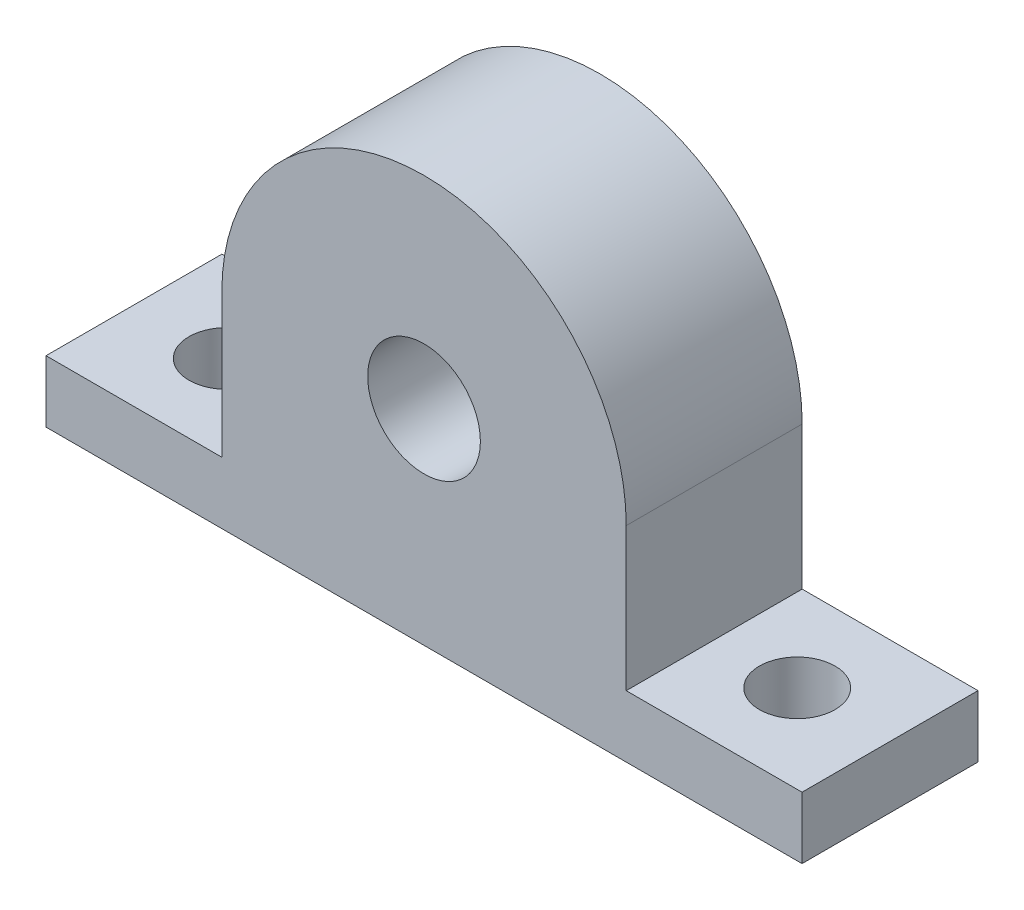
SolidWorks part; units mm, degrees
ref_plane "Front Plane" through (0, 0, 0) normal (0, 0, 1) x (1, 0, 0)
ref_plane "Top Plane" through (0, 0, 0) normal (0, 1, 0) x (1, 0, 0)
ref_plane "Right Plane" through (0, 0, 0) normal (1, 0, 0) x (0, 0, -1)
sketch "Sketch1" plane through (0, 0, 0) normal (0, 0, 1) x (1, 0, 0)
  line L0 (-27.5, 0) -> (27.5, 0)
  line L1 (-27.5, 0) -> (-27.5, 4.5)
  line L2 (-27.5, 4.5) -> (-14.7092, 4.5)
  line L3 (27.5, 0) -> (27.5, 4.5)
  line L4 (27.5, 4.5) -> (14.7092, 4.5)
  line L5 (0, 14.9) -> (0, 3.1442) construction
  line L6 (14.7092, 14.9) -> (14.7092, 3.1442)
  line L7 (-14.7092, 14.9) -> (-14.7092, 3.1442)
  arc A0 (14.7092, 14.9) -> (-14.7092, 14.9) centre (0, 14.9) ccw
  arc A1 (-14.7092, 3.1442) -> (14.7092, 3.1442) centre (0, 3.1442) ccw
  circle A2 centre (0, 14.9) radius 4.1
  point P9 (0, 9.0221)
  point P14 (-12.4629, 14.9)
  point P15 (0, 14.9)
  point P16 (0, 5.7429)
  point P17 (-13.0795, 14.9)
  point P18 (-13.3438, 7.5047)
  point P19 (-13.476, 3.1442)
  point P20 (-14.7092, 14.9)
  dimension "D3" = 8.2
  dimension "D1" = 55
  dimension "D2" = 14.9
  dimension "D4" = 4.5
extrude "Boss-Extrude1" add sketch "Sketch1" along normal blind 12.8
sketch "Sketch2" plane through (0, 0, 0) normal (0, -1, 0) x (1, 0, 0)
  line L0 (20.75, 6.4) -> (-20.75, 6.4) construction
  line L1 (-27.5, 12.8) -> (-27.5, 0) construction
  circle A0 centre (-20.75, 6.4) radius 2.75
  circle A1 centre (20.75, 6.4) radius 2.75
  point P6 (-27.5, 6.4)
  point P7 (0, 6.4)
  dimension "D1" = 5.5
  dimension "D2" = 41.5
extrude "Cut-Extrude1" cut sketch "Sketch2" against normal through all
